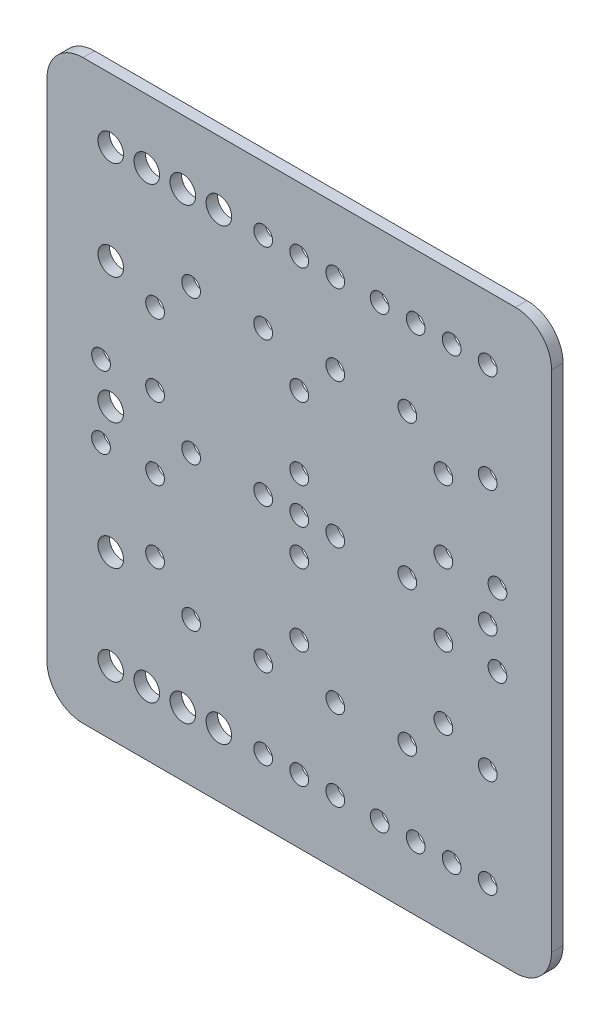
SolidWorks part; units mm, degrees
ref_plane "Front Plane" through (0, 0, 0) normal (0, 0, 1) x (1, 0, 0)
ref_plane "Top Plane" through (0, 0, 0) normal (0, 1, 0) x (1, 0, 0)
ref_plane "Right Plane" through (0, 0, 0) normal (1, 0, 0) x (0, 0, -1)
sketch "Sketch1" plane through (0, 0, 0) normal (0, 0, 1) x (1, 0, 0)
  line L0 (-70, 0) -> (70, 0) construction
  line L1 (-70, 80) -> (70, 80)
  line L2 (-70, 80) -> (-70, -80)
  line L3 (-70, -80) -> (70, -80)
  line L4 (70, 80) -> (70, -80)
  line L5 (0, 0) -> (0, 80) construction
  circle A0 centre (0, 0) radius 2.6
  circle A1 centre (10, 0) radius 2.6
  circle A2 centre (-40, 10) radius 2.6
  circle A3 centre (30, 0) radius 2.6
  circle A4 centre (-10, 0) radius 2.6
  circle A5 centre (40, 10) radius 2.6
  circle A6 centre (-30, 0) radius 2.6
  circle A7 centre (0, 10) radius 2.6
  circle A8 centre (-52.3, 35) radius 3.55
  circle A9 centre (52.3, 35) radius 2.6
  circle A10 centre (22.3, 62.3) radius 2.6
  circle A11 centre (0, 30) radius 2.6
  circle A12 centre (-10, 40) radius 2.6
  circle A13 centre (52.3, 0) radius 2.6
  circle A14 centre (-52.3, 0) radius 3.55
  circle A15 centre (-30, 40) radius 2.6
  circle A16 centre (-52.3, 62.3) radius 3.55
  circle A17 centre (-40, 30) radius 2.6
  circle A18 centre (40, 30) radius 2.6
  circle A19 centre (30, 40) radius 2.6
  circle A20 centre (52.3, 62.3) radius 2.6
  circle A21 centre (10, 40) radius 2.6
  circle A23 centre (-42.3, 62.3) radius 3.55
  circle A24 centre (-32.3, 62.3) radius 3.55
  circle A25 centre (-22.3, -62.3) radius 3.55
  circle A26 centre (55, -10) radius 2.6
  circle A27 centre (42.3, 62.3) radius 2.6
  circle A29 centre (-55, -10) radius 2.6
  circle A30 centre (-10, -62.3) radius 2.6
  circle A31 centre (0, 62.3) radius 2.6
  circle A32 centre (10, 62.3) radius 2.6
  circle A33 centre (-10, 62.3) radius 2.6
  circle A34 centre (10, -62.3) radius 2.6
  circle A35 centre (0, -62.3) radius 2.6
  circle A36 centre (32.3, -62.3) radius 2.6
  circle A37 centre (42.3, -62.3) radius 2.6
  circle A38 centre (-55, 10) radius 2.6
  circle A39 centre (55, 10) radius 2.6
  circle A40 centre (-32.3, -62.3) radius 3.55
  circle A41 centre (-42.3, -62.3) radius 3.55
  circle A42 centre (10, -40) radius 2.6
  circle A43 centre (52.3, -62.3) radius 2.6
  circle A44 centre (30, -40) radius 2.6
  circle A45 centre (40, -30) radius 2.6
  circle A46 centre (-40, -30) radius 2.6
  circle A47 centre (-52.3, -62.3) radius 3.55
  circle A48 centre (-30, -40) radius 2.6
  circle A49 centre (-10, -40) radius 2.6
  circle A50 centre (-22.3, 62.3) radius 3.55
  circle A51 centre (0, -30) radius 2.6
  circle A52 centre (32.3, 62.3) radius 2.6
  circle A53 centre (0, 30) radius 2.6 [skipped]
  circle A54 centre (0, 20) radius 2.6 [skipped]
  circle A55 centre (-52.3, 31.15) radius 3.55 [skipped]
  circle A56 centre (52.3, 31.15) radius 2.6 [skipped]
  circle A57 centre (-20, 0) radius 2.6 [skipped]
  circle A58 centre (20, 0) radius 2.6 [skipped]
  circle A59 centre (22.3, -62.3) radius 2.6
  circle A60 centre (52.3, -35) radius 2.6
  circle A61 centre (-52.3, -35) radius 3.55
  circle A62 centre (0, -10) radius 2.6
  circle A63 centre (40, -10) radius 2.6
  circle A64 centre (-40, -10) radius 2.6
  circle A65 centre (32.3, 62.3) radius 2.6 [skipped]
  point P0 (0, 0)
  point P6 (-70, 0)
  point P7 (70, 0)
  point P8 (0, 80)
  dimension "D3" = 5.2
  dimension "D9" = 7.1
  dimension "D1" = 160
  dimension "D2" = 140
  dimension "D7" = 55
  dimension "D8" = 40
  dimension "D12" = 35
  dimension "D15" = 17.7
  dimension "D17" = 17.7
  dimension "D18" = 17.7
  dimension "D19" = 10
  dimension "D20" = 30
  dimension "D21" = 10
  dimension "D22" = 40
  dimension "D23" = 10
  dimension "D24" = 10
  dimension "D25" = 10
  dimension "D26" = 20
  dimension "D27" = 3
  dimension "D28" = 55
  dimension "D29" = 10
  dimension "D6" = 40
  dimension "D10" = 4
  dimension "D4" = 4
  dimension "D5" = 4
  dimension "D11" = 3
  dimension "D13" = 3
  dimension "D14" = 3
extrude "Boss-Extrude1" add sketch "Sketch1" against normal blind 3.2
fillet "Fillet1" radius 10 4 edges at (-70, -80, -1.6) (70, -80, -1.6) (70, 80, -1.6) (-70, 80, -1.6)
